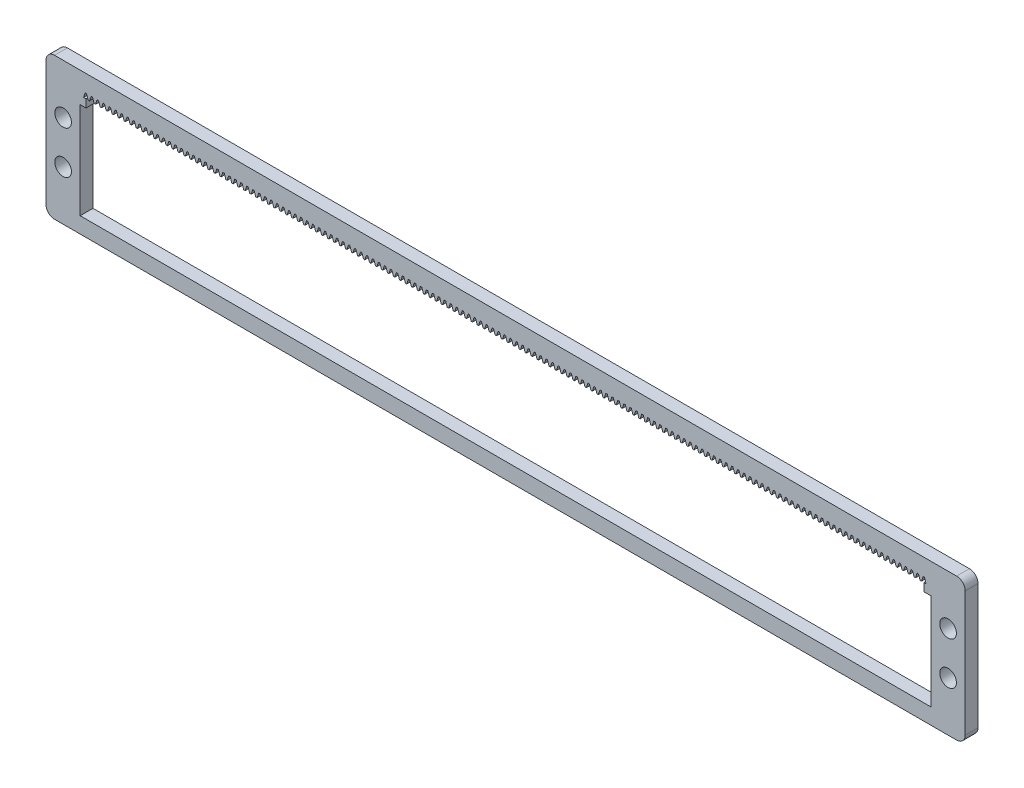
SolidWorks part; units mm, degrees
other "Markup1"
sketch "Sketch6" plane through (0, -30, 3.6) normal (0, 0, 1) x (1, 0, 0)
other "Markup2"
sketch "Sketch7" plane through (0, -30, 3.6) normal (0, 0, 1) x (1, 0, 0)
ref_plane "Front Plane" through (0, 0, 0) normal (0, 0, 1) x (1, 0, 0)
ref_plane "Top Plane" through (0, 0, 0) normal (0, 1, 0) x (1, 0, 0)
ref_plane "Right Plane" through (0, 0, 0) normal (1, 0, 0) x (0, 0, -1)
sketch "Sketch1" plane through (0, 0, 0) normal (0, 0, 1) x (1, 0, 0)
  line L1 (2, 0) -> (213, 0)
  line L2 (0, -2) -> (0, -31.22)
  line L3 (2, -33.22) -> (213, -33.22)
  line L4 (215, -2) -> (215, -31.22)
  arc A0 (213, -33.22) -> (215, -31.22) centre (213, -31.22) ccw
  arc A1 (0, -31.22) -> (2, -33.22) centre (2, -31.22) ccw
  arc A2 (2, 0) -> (0, -2) centre (2, -2) ccw
  arc A3 (213, 0) -> (215, -2) centre (213, -2) cw
  point P7 (215, -33.22)
  point P12 (0, 0)
  point P15 (215, 0)
  dimension "D3" = 2
  dimension "D1" = 33.22
  dimension "D2" = 215
extrude "Boss-Extrude1" add sketch "Sketch1" along normal blind 3
sketch "Sketch2" plane through (0, 0, 3) normal (0, 0, 1) x (1, 0, 0)
  line L0 (2, -33.22) -> (213, -33.22) construction
  line L1 (8, -7) -> (207, -7)
  line L2 (8, -7) -> (8, -29.5)
  line L3 (8, -29.5) -> (207, -29.5)
  line L4 (207, -7) -> (207, -29.5)
  line L5 (0, -2) -> (0, -31.22) construction
  line L7 (215, -31.22) -> (215, -2) construction
  line L8 (8, -18.25) -> (207, -18.25) construction
  line L12 (8, -29.5) -> (207, -29.5) construction
  line L13 (207, -4.3144) -> (207, -29.5) construction
  dimension "D1" = 22.5
  dimension "D2" = 8
  dimension "D3" = 8
  dimension "D4" = 3.72
extrude "Cut-Extrude1" cut sketch "Sketch2" against normal through all
sketch "Sketch3" plane through (0, 0, 3) normal (0, 0, 1) x (1, 0, 0)
  line L0 (207, -7) -> (8, -7) construction
  line L1 (9.35, -7) -> (205.32, -7)
  line L2 (9.35, -7) -> (9.35, -5.15)
  line L3 (9.35, -5.15) -> (205.32, -5.15)
  line L4 (205.32, -7) -> (205.32, -5.15)
  line L5 (207, -29.5) -> (207, -7) construction
  line L6 (8, -7) -> (8, -29.5) construction
  dimension "D1" = 1.85
  dimension "D2" = 1.68
  dimension "D3" = 1.35
extrude "Cut-Extrude2" cut sketch "Sketch3" against normal through all
sketch "Sketch4" plane through (0, 0, 3) normal (0, 0, 1) x (1, 0, 0)
  line L0 (206.345, -5.15) -> (205.865, -5.15) construction
  line L1 (205.32, -5.15) -> (9.35, -5.15) construction
  line L2 (206.345, -5.15) -> (206.725, -4.0118) construction
  line L3 (206.725, -4.0118) -> (205.485, -4.0118) construction
  line L4 (205.485, -4.0118) -> (205.865, -5.15)
  line L5 (205.485, -4.0118) -> (205.155, -4.0118)
  line L6 (205.155, -4.0118) -> (204.775, -5.15)
  line L7 (204.775, -5.15) -> (205.865, -5.15)
  line L10 (205.865, -5.15) -> (206.345, -5.15) construction
  dimension "D1" = 0.48
  dimension "D2" = 1.2
  dimension "D3" = 1.2
  dimension "D4" = 0.33
  dimension "D5" = 1.24
  dimension "D6" = 1.2
extrude "Cut-Extrude4" cut sketch "Sketch4" against normal through all
pattern_linear "LPattern1" count 141 spacing 1.4 along (-1, 0, 0) of "Cut-Extrude4"
sketch "Sketch5" plane through (0, 0, 3) normal (0, 0, 1) x (1, 0, 0)
  line L0 (207, -16.61) -> (215, -16.61) construction
  line L1 (213, 0) -> (2, 0) construction
  line L2 (8, -7) -> (8, -29.5) construction
  line L3 (0, -2) -> (0, -31.22) construction
  line L4 (2, -33.22) -> (213, -33.22) construction
  line L5 (0, -16.61) -> (8, -16.61) construction
  line L7 (211, -11.61) -> (211, -21.61) construction
  line L8 (4, -11.61) -> (4, -21.61) construction
  line L9 (207, -29.5) -> (207, -7) construction
  line L10 (215, -31.22) -> (215, -2) construction
  circle A4 centre (4, -11.61) radius 1.95
  circle A5 centre (4, -21.61) radius 1.95
  circle A6 centre (211, -11.61) radius 1.95
  circle A7 centre (211, -21.61) radius 1.95
  point P8 (211, -16.61)
  point P18 (4, -16.61)
  point P22 (4, -16.61)
  point P31 (211, -16.61)
  dimension "D1" = 3.9
  dimension "D3" = 3.9
  dimension "D4" = 3.9
  dimension "D6" = 3.9
  dimension "D5" = 10
  dimension "D7" = 10
extrude "Cut-Extrude5" cut sketch "Sketch5" against normal blind 10
